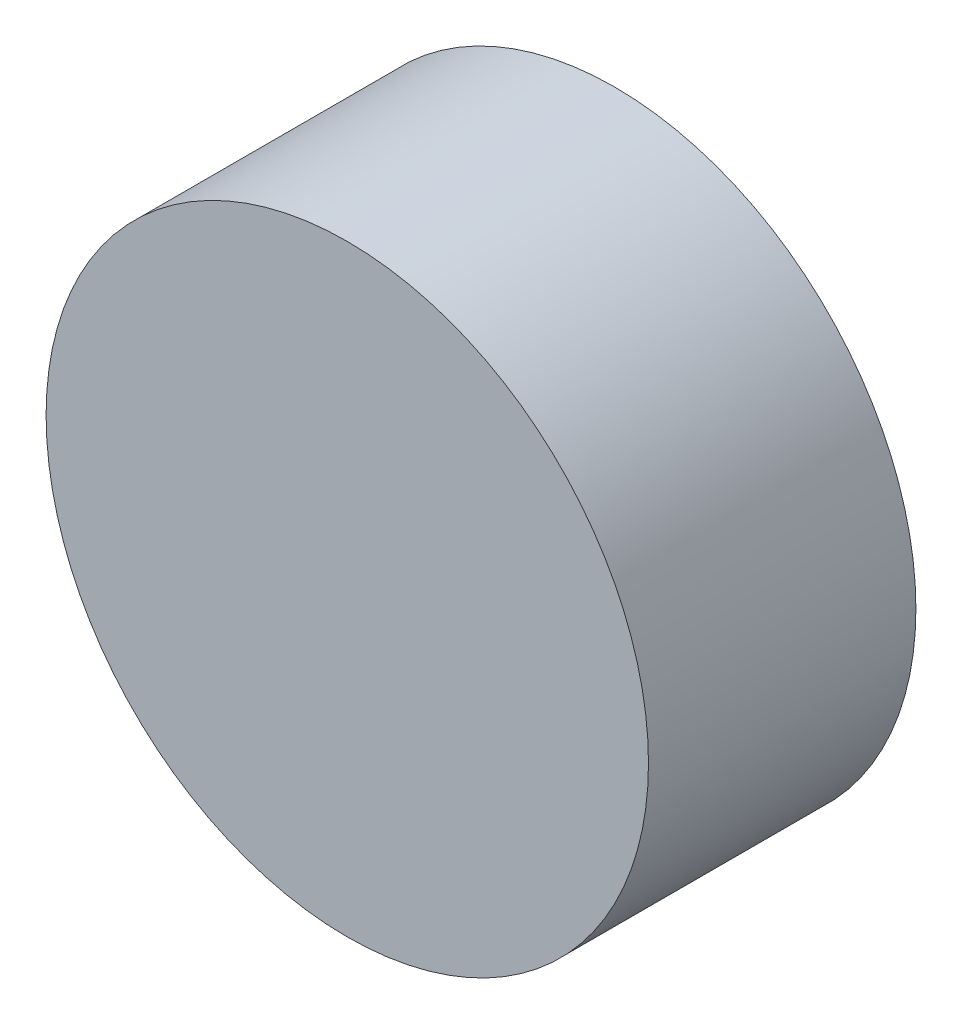
SolidWorks part; units mm, degrees
material "Filter_Bulk_6061Properties"
ref_plane "Front Plane" through (0, 0, 0) normal (0, 0, 1) x (1, 0, 0)
ref_plane "Top Plane" through (0, 0, 0) normal (0, 1, 0) x (1, 0, 0)
ref_plane "Right Plane" through (0, 0, 0) normal (1, 0, 0) x (0, 0, -1)
sketch "Sketch1" plane through (0, 0, 0) normal (0, 0, 1) x (1, 0, 0)
  circle A0 centre (0, 0) radius 12.8397
  circle A1 centre (0, 0) radius 12.8397 construction
extrude "Boss-Extrude1" add sketch "Sketch1" along normal blind 11.4
